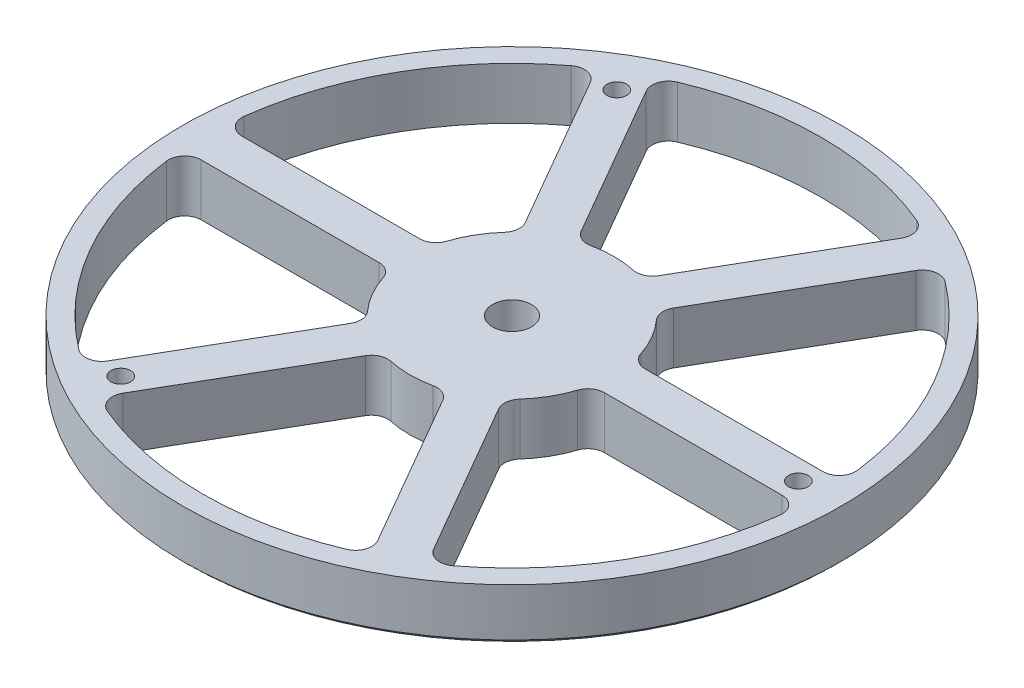
SolidWorks part; units mm, degrees
material "6061-T6 (SS)"
ref_plane "Front Plane" through (0, 0, 0) normal (0, 0, 1) x (1, 0, 0)
ref_plane "Top Plane" through (0, 0, 0) normal (0, 1, 0) x (1, 0, 0)
ref_plane "Right Plane" through (0, 0, 0) normal (1, 0, 0) x (0, 0, -1)
sketch "Sketch2" plane through (0, 0, 0) normal (1, 0, 0) x (0, 0, -1)
  line L0 (0, 0) -> (-80.55, 0)
  line L1 (-80.55, 0) -> (-80.55, 12.7)
  line L2 (-80.55, 12.7) -> (0, 12.7)
  line L5 (0, 12.7) -> (0, 0)
  dimension "D1" = 80.55
  dimension "D2" = 12.7
ref_axis "Axis1" through (0, -0.635, 0) along (0, 1, 0)
revolve "Revolve1" add sketch "Sketch2" angle 360 about axis through (0, -0.635, 0) along (0, 1, 0)
hole_wizard "#12 (0.189) Diameter Hole1" positions "Sketch6" profile "Sketch7" hole size "#12" standard "ANSI Inch" end condition through all
sketch "Sketch6" plane through (0, 12.7, 0) normal (0, 1, 0) x (1, 0, 0)
  line L0 (0, 0) -> (-69.8201, 120.932) construction
  line L2 (0, 0) -> (0, 109.0908) construction
  point P0 (-35, 60.6218)
  dimension "D1" = 30
  dimension "D2" = 70
sketch "Sketch7" plane through (-35, 12.7, -60.6218) normal (1, 0, 0) x (0, 0, 1)
  line L0 (0, 0) -> (0, 12.7)
  line L1 (0, 12.7) -> (2.4003, 12.7)
  line L2 (2.4003, 12.7) -> (2.4003, 0)
  line L5 (2.4003, 0) -> (0, 0)
  line L11 (0, -6.35) -> (0, 107.95) construction
  dimension "Thru Hole Dia." = 4.8006
  dimension "Thru Hole Depth" = 12.7
pattern_circular "CirPattern3" count 3 over 360 about axis through (0, 0, 0) along (0, 1, 0) of "#12 (0.189) Diameter Hole1"
sketch "Sketch8" plane through (0, 12.7, 0) normal (0, 1, 0) x (1, 0, 0)
  line L4 (0, 0) -> (0, 93.9995) construction
  line L5 (0, 0) -> (113.8372, 0) construction
  line L6 (-7.9173, 23.7132) -> (-33.3621, 67.7848)
  line L7 (7.9173, 23.7132) -> (33.3621, 67.7848)
  line L8 (0, 0) -> (-35, 60.6218) construction
  arc A0 (-7.9173, 23.7132) -> (7.9173, 23.7132) centre (0, 0) cw
  arc A1 (-33.3621, 67.7848) -> (33.3621, 67.7848) centre (0, 0) cw
  circle A2 centre (0, 0) radius 80.55 construction
  dimension "D1" = 25
  dimension "D2" = 5
  dimension "D3" = 5
extrude "Cut-Extrude1" cut sketch "Sketch8" against normal through all
fillet "Fillet1" radius 4 4 edges at (7.9173, 6.35, -23.7132) (33.3621, 6.35, -67.7848) (-7.9173, 6.35, -23.7132) (-33.3621, 6.35, -67.7848)
pattern_circular "CirPattern4" count 6 over 360 about axis through (0, 0, 0) along (0, 1, 0) of "Cut-Extrude1", "Fillet1"
chamfer "Chamfer2" distance 1 angle 45 1 edges at (0, 0, -80.55)
hole_wizard "3/8 (0.375) Diameter Hole1" positions "Sketch9" profile "Sketch11" hole size "3/8" standard "ANSI Inch" end condition through all
sketch "Sketch9" plane through (0, 0, 0) normal (0, -1, 0) x (-1, 0, 0)
  point P0 (0, 0)
sketch "Sketch11" plane through (0, 0, 0) normal (1, 0, 0) x (0, 0, -1)
  line L0 (0, 0) -> (0, 12.7)
  line L1 (0, 12.7) -> (4.7625, 12.7)
  line L2 (4.7625, 12.7) -> (4.7625, 0)
  line L5 (4.7625, 0) -> (0, 0)
  line L11 (0, -6.35) -> (0, 107.95) construction
  dimension "Thru Hole Dia." = 9.525
  dimension "Thru Hole Depth" = 12.7
equation "\"TubeDiameter\" = 6.500in"
equation "\"D1@Sketch2\"=(\"TubeDiameter\"-4)/2"
